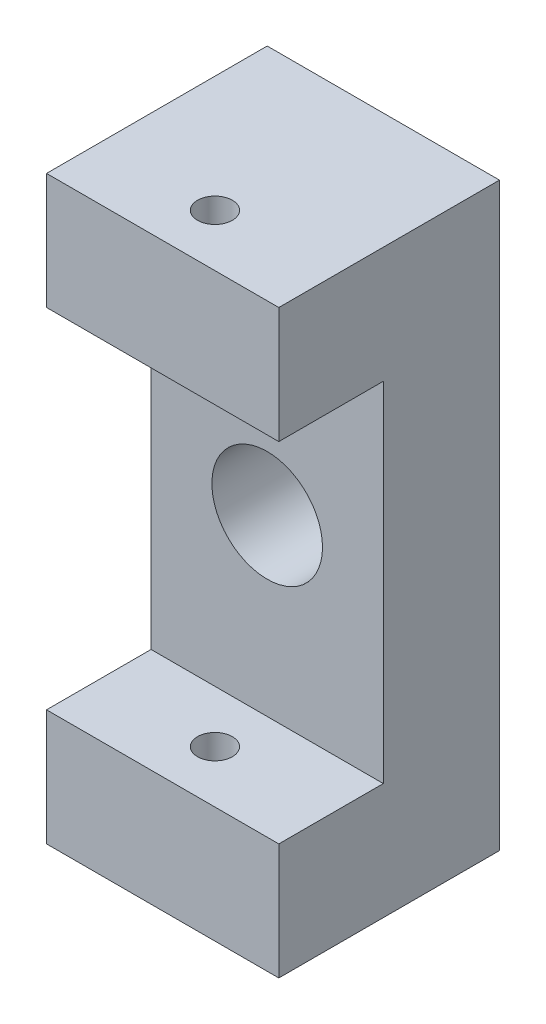
SolidWorks part; units mm, degrees
material "ABS"
ref_plane "Front Plane" through (0, 0, 0) normal (0, 0, 1) x (1, 0, 0)
ref_plane "Top Plane" through (0, 0, 0) normal (0, 1, 0) x (1, 0, 0)
ref_plane "Right Plane" through (0, 0, 0) normal (1, 0, 0) x (0, 0, -1)
sketch "Sketch1" plane through (0, 0, 0) normal (0, 0, 1) x (1, 0, 0)
  line L0 (10, 30) -> (10, 0) construction
  line L1 (0, 0) -> (20, 0)
  line L2 (0, 0) -> (0, 30)
  line L3 (0, 30) -> (20, 30)
  line L4 (20, 0) -> (20, 30)
  line L5 (0, 15) -> (20, 15) construction
  line L6 (0, 30) -> (0, 40)
  line L7 (0, 40) -> (20, 40)
  line L8 (20, 40) -> (20, 30)
  line L9 (0, 0) -> (0, -10)
  line L10 (0, -10) -> (20, -10)
  line L11 (20, -10) -> (20, 0)
  circle A0 centre (10, 15) radius 4.7625
  dimension "D3" = 9.525
  dimension "D1" = 30
  dimension "D2" = 20
  dimension "D4" = 10
  dimension "D5" = 10
extrude "Boss-Extrude1" add sketch "Sketch1" along normal blind 10 contours L1 L4 L3 L2 A0
sketch "Sketch2" plane through (0, 0, 0) normal (0, 0, 1) x (1, 0, 0)
  line L0 (20, -10) -> (20, 0) construction
  line L1 (0, -10) -> (20, -10) construction
  line L2 (0, 0) -> (0, -10) construction
  line L3 (20, 40) -> (20, 30) construction
  line L4 (0, 40) -> (20, 40) construction
  line L5 (0, 30) -> (0, 40) construction
  line L6 (20, -10) -> (20, 0)
  line L7 (0, -10) -> (20, -10)
  line L8 (0, 0) -> (0, -10)
  line L9 (20, 40) -> (20, 30)
  line L10 (0, 40) -> (20, 40)
  line L11 (0, 30) -> (0, 40)
  line L12 (0, 30) -> (20, 30)
  line L13 (0, 0) -> (20, 0)
extrude "Boss-Extrude2" add sketch "Sketch2" along normal blind 19
sketch "Sketch3" plane through (0, 40, 0) normal (0, 1, 0) x (1, 0, 0)
  line L0 (0, -14.5) -> (20, -14.5) construction
  line L1 (0, -19) -> (0, 0) construction
  line L2 (20, -19) -> (20, 0) construction
  line L3 (10, 0) -> (10, -19) construction
  line L4 (0, 0) -> (20, 0) construction
  line L5 (20, -19) -> (0, -19) construction
  line L6 (0, -10) -> (20, -10) construction
  line L7 (0, -10) -> (20, -10)
  circle A0 centre (10, -14.5) radius 1.5
  point P12 (10, -14.5)
  point P25 (10, -14.5)
  dimension "D2" = 3
  dimension "D1" = 4.5
extrude "Cut-Extrude1" cut sketch "Sketch3" against normal through all contours A0
